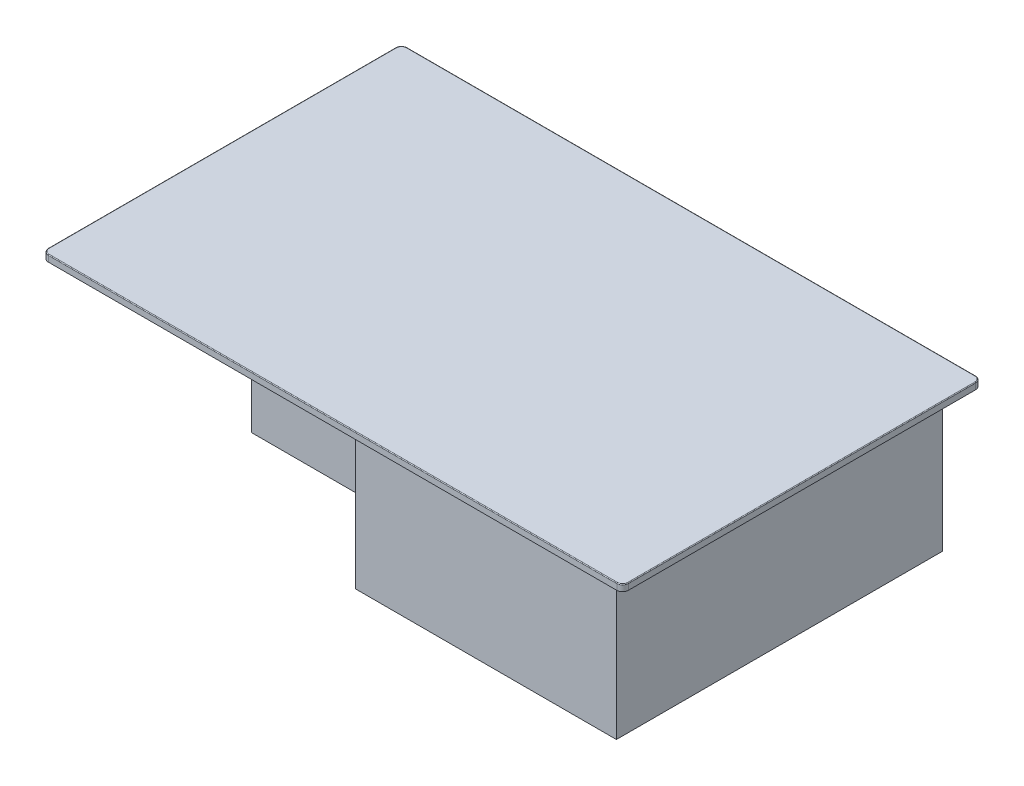
SolidWorks part; units mm, degrees
ref_plane "Front Plane" through (0, 0, 0) normal (0, 0, 1) x (1, 0, 0)
ref_plane "Top Plane" through (0, 0, 0) normal (0, 1, 0) x (1, 0, 0)
ref_plane "Right Plane" through (0, 0, 0) normal (1, 0, 0) x (0, 0, -1)
sketch "Sketch1" plane through (0, 0, 0) normal (0, 1, 0) x (1, 0, 0)
  line L1 (400, -247.5) -> (-400, -247.5)
  line L2 (400, -247.5) -> (400, 247.5)
  line L3 (400, 247.5) -> (-400, 247.5)
  line L4 (-400, -247.5) -> (-400, 247.5)
  line L5 (400, -247.5) -> (-400, 247.5) construction
  line L6 (400, 247.5) -> (-400, -247.5) construction
  point P0 (0, 0)
  dimension "D1" = 800
  dimension "D2" = 495
extrude "Boss-Extrude1" add sketch "Sketch1" against normal blind 9
fillet "Fillet1" radius 8 4 edges at (400, -4.5, -247.5) (-400, -4.5, -247.5) (-400, -4.5, 247.5) (400, -4.5, 247.5)
fillet "Fillet2" radius 1 8 edges at (397.6569, 0, 245.1569) (0, 0, 247.5) (-397.6569, 0, 245.1569) (-400, 0, 0) (-397.6569, 0, -245.1569) (0, 0, -247.5) (397.6569, 0, -245.1569) (400, 0, 0)
sketch "Sketch2" plane through (0, -9, 0) normal (0, -1, 0) x (1, 0, 0)
  line L1 (387.5, -236) -> (-387.5, -236)
  line L2 (387.5, -236) -> (387.5, 236)
  line L3 (387.5, 236) -> (-387.5, 236)
  line L4 (-387.5, -236) -> (-387.5, 236)
  line L5 (387.5, -236) -> (-387.5, 236) construction
  line L6 (387.5, 236) -> (-387.5, -236) construction
  point P0 (0, 0)
  dimension "D1" = 775
  dimension "D2" = 472
extrude "Boss-Extrude2" add sketch "Sketch2" along normal blind 4
sketch "Sketch3" plane through (0, 0, 0) normal (0, 1, 0) x (1, 0, 0)
  line L0 (-399, 239.5) -> (-399, -239.5) construction
  line L1 (1, -190) -> (-169, -190)
  line L2 (1, -190) -> (1, 190)
  line L3 (1, 190) -> (-169, 190)
  line L4 (-169, -190) -> (-169, 190)
  line L5 (1, -190) -> (-169, 190) construction
  line L6 (1, 190) -> (-169, -190) construction
  point P0 (-84, 0)
  dimension "D1" = 170
  dimension "D2" = 380
  dimension "D3" = 230
extrude "Boss-Extrude3" add sketch "Sketch3" against normal blind 130
sketch "Sketch4" plane through (0, 0, 0) normal (0, 1, 0) x (1, 0, 0)
  line L0 (399, -239.5) -> (399, 239.5) construction
  line L1 (369, -225) -> (9, -225)
  line L2 (369, -225) -> (369, 225)
  line L3 (369, 225) -> (9, 225)
  line L4 (9, -225) -> (9, 225)
  line L5 (369, -225) -> (9, 225) construction
  line L6 (369, 225) -> (9, -225) construction
  point P0 (189, 0)
  dimension "D1" = 450
  dimension "D2" = 360
  dimension "D3" = 30
extrude "Boss-Extrude4" add sketch "Sketch4" against normal blind 210
